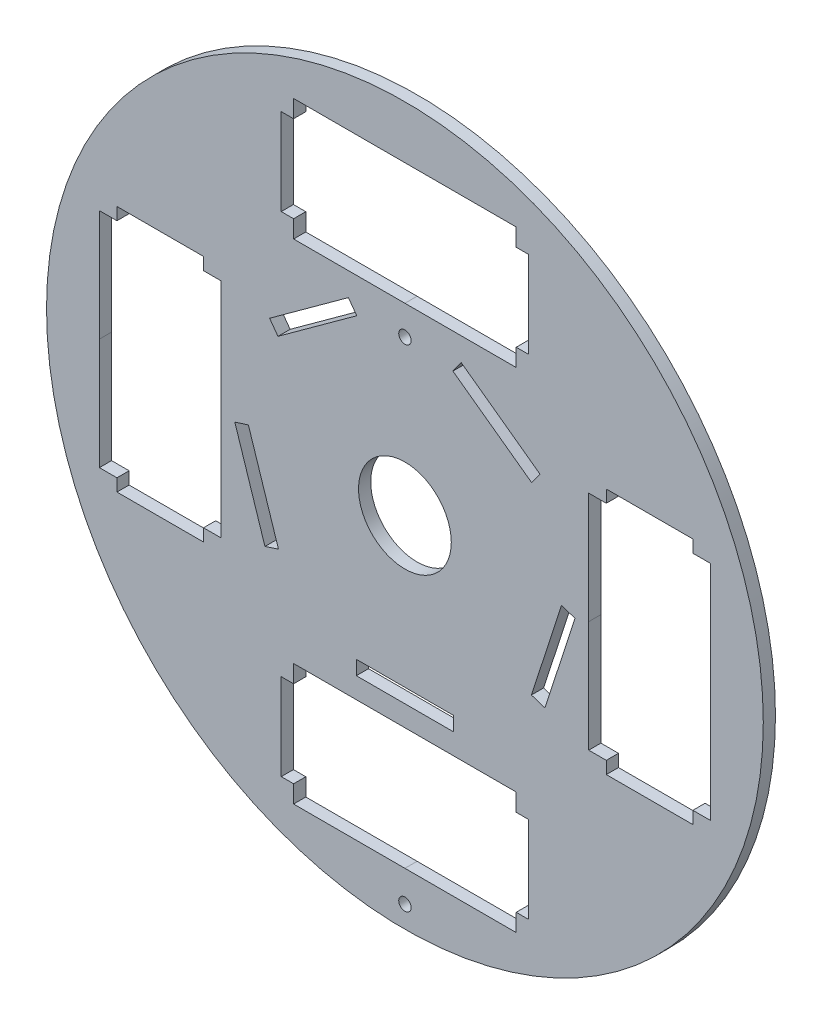
SolidWorks part; units mm, degrees
material "Pine"
ref_plane "Front Plane" through (0, 0, 0) normal (0, 0, 1) x (1, 0, 0)
ref_plane "Top Plane" through (0, 0, 0) normal (0, 1, 0) x (1, 0, 0)
ref_plane "Right Plane" through (0, 0, 0) normal (1, 0, 0) x (0, 0, -1)
sketch "Model" plane through (0, 0, 0) normal (0, 0, 1) x (1, 0, 0)
  line L0 (75.0973, -195.6366) -> (75.0973, -149.9166)
  line L1 (170.6519, -211.0416) -> (130.6515, -211.0416)
  line L2 (67.8806, -99.1166) -> (67.8806, -104.1966)
  line L3 (67.8806, -99.1166) -> (32.3206, -99.1164)
  line L4 (32.3201, -200.7164) -> (32.3202, -195.6364)
  line L5 (25.1031, -195.6364) -> (32.3202, -195.6364)
  line L6 (75.0977, -104.1966) -> (67.8806, -104.1966)
  line L7 (25.1031, -195.6364) -> (25.1035, -149.9164)
  line L8 (75.0973, -195.6366) -> (67.8802, -195.6366)
  line L9 (25.1035, -104.1964) -> (25.1035, -149.9164)
  line L10 (25.1035, -104.1964) -> (32.3206, -104.1964)
  line L11 (67.8801, -200.7166) -> (32.3201, -200.7164)
  line L12 (67.8801, -200.7166) -> (67.8802, -195.6366)
  line L13 (93.1124, -189.6731) -> (80.7516, -151.6305)
  line L14 (98.6684, -187.8678) -> (93.1124, -189.6731)
  line L15 (98.6684, -187.8678) -> (86.3077, -149.8252)
  line L16 (80.7516, -151.6305) -> (86.3077, -149.8252)
  line L17 (95.0301, -107.5201) -> (127.3911, -84.0085)
  line L18 (196.3284, -225.4273) -> (150.6084, -225.4273)
  line L19 (99.8084, -232.644) -> (104.8884, -232.644)
  line L20 (99.8084, -232.644) -> (99.8082, -268.204)
  line L21 (201.4082, -268.2044) -> (196.3282, -268.2044)
  line L22 (196.3282, -275.4215) -> (196.3282, -268.2044)
  line L23 (104.8884, -225.4269) -> (104.8884, -232.644)
  line L24 (196.3282, -275.4215) -> (150.6082, -275.4211)
  line L25 (196.3284, -225.4273) -> (196.3284, -232.6444)
  line L26 (104.8882, -275.4211) -> (150.6082, -275.4211)
  line L27 (104.8882, -275.4211) -> (104.8882, -268.204)
  line L28 (201.4084, -232.6444) -> (201.4082, -268.2044)
  line L29 (201.4084, -232.6444) -> (196.3284, -232.6444)
  line L30 (98.464, -112.2464) -> (95.0301, -107.5201)
  line L31 (99.8082, -268.204) -> (104.8882, -268.204)
  line L32 (104.8884, -225.4269) -> (150.6084, -225.4273)
  line L33 (32.3206, -99.1164) -> (32.3206, -104.1964)
  line L34 (75.0977, -104.1966) -> (75.0973, -149.9166)
  line L35 (104.888, -74.4054) -> (150.608, -74.4054)
  line L36 (201.408, -67.1888) -> (196.328, -67.1887)
  line L37 (201.408, -67.1888) -> (201.4082, -31.6288)
  line L38 (99.8082, -31.6283) -> (104.8882, -31.6284)
  line L39 (104.8882, -24.4113) -> (104.8882, -31.6284)
  line L40 (196.328, -74.4058) -> (196.328, -67.1887)
  line L41 (104.8882, -24.4113) -> (150.6082, -24.4116)
  line L42 (104.888, -74.4054) -> (104.888, -67.1884)
  line L43 (196.3282, -24.4116) -> (150.6082, -24.4116)
  line L44 (196.3282, -24.4116) -> (196.3282, -31.6287)
  line L45 (99.808, -67.1883) -> (99.8082, -31.6283)
  line L46 (99.808, -67.1883) -> (104.888, -67.1884)
  line L47 (98.464, -112.2464) -> (130.8249, -88.7348)
  line L48 (127.3911, -84.0085) -> (130.8249, -88.7348)
  line L49 (201.4082, -31.6288) -> (196.3282, -31.6287)
  line L50 (196.328, -74.4058) -> (150.608, -74.4054)
  line L51 (226.1191, -104.1962) -> (226.1191, -149.9162)
  line L52 (233.3358, -200.7162) -> (233.3358, -195.6362)
  line L53 (233.3358, -200.7162) -> (268.8958, -200.7163)
  line L54 (268.8962, -99.1163) -> (268.8962, -104.1963)
  line L55 (276.1133, -104.1964) -> (268.8962, -104.1963)
  line L56 (170.6519, -216.8836) -> (130.6515, -216.8836)
  line L57 (130.6515, -216.8836) -> (130.6515, -211.0416)
  line L58 (226.1187, -195.6362) -> (233.3358, -195.6362)
  line L59 (170.6519, -211.0416) -> (170.6519, -216.8836)
  line L60 (276.1133, -104.1964) -> (276.1129, -149.9164)
  line L61 (226.1191, -104.1962) -> (233.3362, -104.1962)
  line L62 (276.1129, -195.6364) -> (276.1129, -149.9164)
  line L63 (276.1129, -195.6364) -> (268.8958, -195.6363)
  line L64 (233.3362, -99.1162) -> (268.8962, -99.1163)
  line L65 (233.3362, -99.1162) -> (233.3362, -104.1962)
  line L66 (173.7549, -83.9573) -> (206.1158, -107.4689)
  line L67 (170.321, -88.6836) -> (173.7549, -83.9573)
  line L68 (268.8958, -200.7163) -> (268.8958, -195.6363)
  line L69 (226.1187, -195.6362) -> (226.1191, -149.9162)
  line L82 (170.321, -88.6836) -> (202.682, -112.1952)
  line L83 (206.1158, -107.4689) -> (202.682, -112.1952)
  line L84 (220.4917, -151.5477) -> (208.1309, -189.5903)
  line L85 (214.9356, -149.7424) -> (220.4917, -151.5477)
  line L86 (214.9356, -149.7424) -> (202.5748, -187.785)
  line L87 (208.1309, -189.5903) -> (202.5748, -187.785)
  circle A0 centre (150.6082, -288.1784) radius 2.54
  circle A1 centre (150.6082, -149.9164) radius 147.2209
  circle A2 centre (150.6082, -149.9164) radius 19.05
  circle A3 centre (150.6084, -86.4355) radius 2.54
extrude "Boss-Extrude1" add sketch "Model" along normal blind 5.0038
